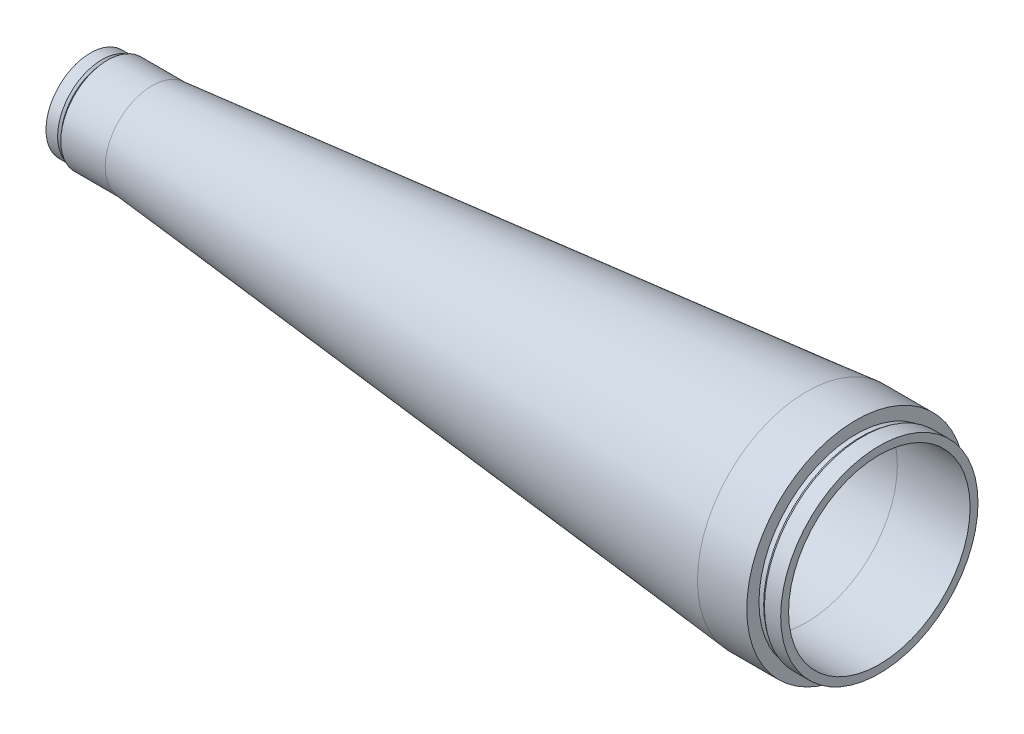
SolidWorks part; units mm, degrees
material "3.1645 (EN-AW 2030)"
ref_plane "Přední rovina" through (0, 0, 0) normal (0, 0, 1) x (1, 0, 0)
ref_plane "Horní rovina" through (0, 0, 0) normal (0, 1, 0) x (1, 0, 0)
ref_plane "Pravá rovina" through (0, 0, 0) normal (1, 0, 0) x (0, 0, -1)
sketch "Skica1" plane through (0, 0, 0) normal (0, 0, 1) x (1, 0, 0)
  line L0 (-36.7133, 44.25) -> (-36.7133, -44.25) construction
  line L1 (-36.7133, 44.25) -> (-36.7133, -38.9168) construction
  line L2 (-172.4424, 0) -> (-98.619, 0) construction
  line L3 (-36.7133, -44.25) -> (-56.7133, -44.25)
  line L7 (-322.05, -12.9) -> (-217.05, -23.4)
  line L9 (-212.6322, -25.6) -> (-117.05, -29.4)
  line L10 (-117.05, -29.4) -> (-117.05, -33.4)
  line L12 (-56.7133, -36.8) -> (-27.2133, -36.8)
  line L13 (-27.2133, -36.8) -> (-27.2133, -40)
  line L14 (-27.2133, -40) -> (-33.8133, -40)
  line L15 (-36.7133, -39.3) -> (-36.7133, -44.25)
  line L16 (-26.7133, 38.094) -> (-26.7133, -38.094) construction
  line L17 (-56.7133, -44.25) -> (-56.7133, -36.8) construction
  line L19 (-34.8133, -39.3) -> (-36.7133, -39.3)
  line L21 (-34.8133, -39.3) -> (-33.8133, -40)
  line L22 (-506.9511, 0) -> (94.0461, 0) construction
  line L23 (-115.55, -33.4) -> (-117.05, -33.4)
  line L24 (-117.05, 27.4) -> (-117.05, -27.4) construction
  line L27 (-112.0997, -33.4124) -> (-56.7133, -36.8)
  line L28 (-217.05, -19.7) -> (-217.05, 19.7) construction
  line L29 (-117.05, -27.4) -> (-115.05, -29.4) construction
  line L34 (-115.05, -33.4) -> (-117.05, -33.4) construction
  line L35 (-115.05, -33.4) -> (-115.05, -29.4) construction
  line L37 (-117.05, -33.4) -> (-117.05, -27.4) construction
  line L40 (-115.55, -33.4) -> (-115.55, -34.5)
  line L41 (-115.55, -34.5) -> (-113.1873, -34.5)
  line L42 (-113.1873, -34.5) -> (-112.0997, -33.4124)
  line L43 (-113.45, -34.1) -> (-113.45, -30.9) construction
  line L44 (-36.7133, -39.3) -> (-36.7133, -44.25) construction
  line L45 (-217.05, -23.4) -> (-217.05, -25.4)
  line L46 (-217.05, -25.4) -> (-215.55, -25.4)
  line L47 (-215.55, -25.4) -> (-215.55, -26.9)
  line L48 (-215.55, -26.9) -> (-213.9322, -26.9)
  line L49 (-213.9322, -26.9) -> (-212.6322, -25.6)
  line L50 (-217.05, -25.4) -> (-215.05, -25.4) construction
  line L51 (-215.05, -25.4) -> (-215.05, -21.7) construction
  line L52 (-215.05, -21.7) -> (-217.05, -19.7) construction
  line L53 (-217.05, -19.7) -> (-217.05, -25.4) construction
  line L54 (-213.8, -26.25) -> (-213.8, -23.75) construction
  line L55 (-347.05, -18) -> (-342.35, -18)
  line L56 (-322.05, -19) -> (-56.7133, -44.25)
  line L57 (-322.05, -9.65) -> (-322.05, 9.65) construction
  line L59 (-322.05, -12.9) -> (-322.05, -15.4)
  line L60 (-322.05, -15.4) -> (-323.75, -15.4)
  line L61 (-323.75, -15.4) -> (-323.75, -16.5)
  line L62 (-323.75, -16.5) -> (-324.9642, -16.5)
  line L63 (-324.9642, -16.5) -> (-325.9642, -15.5)
  line L64 (-325.9642, -15.5) -> (-345.05, -15.5)
  line L65 (-322.05, -15.4) -> (-322.05, -9.65) construction
  line L66 (-322.05, -9.65) -> (-324.05, -11.65) construction
  line L67 (-324.05, -11.65) -> (-324.05, -15.4) construction
  line L68 (-324.05, -15.4) -> (-322.05, -15.4) construction
  line L69 (-325.05, -16) -> (-325.05, -14) construction
  line L70 (-325.05, -15) -> (-325.9642, -15.5) construction
  line L71 (-347.05, 6) -> (-347.05, -6) construction
  line L72 (-347.05, -15.5) -> (-347.05, -18)
  line L75 (-345.05, -15.5) -> (-347.05, -15.5)
  line L76 (-340.05, -19) -> (-340.05, -17.3)
  line L77 (-340.05, -17.3) -> (-341.55, -17.3)
  line L78 (-341.55, -17.3) -> (-342.35, -18)
  line L79 (-340.05, -19) -> (-322.05, -19)
  arc A0 (-15.7133, 37.5) -> (-15.7133, -37.5) centre (509.65, 0) ccw construction
  arc A1 (-15.7133, 37.5) -> (-15.7133, -37.5) centre (509.65, 0) ccw construction
  circle A3 centre (-213.8, -25) radius 1.25 construction
  circle A4 centre (-113.45, -32.5) radius 1.6 construction
  circle A5 centre (-325.05, -15) radius 1 construction
  point P28 (-17.05, 0)
  point P31 (-217.05, 0)
  point P32 (-117.05, 0)
  point P55 (-322.05, 0)
  point P69 (-347.05, 0)
  dimension "D7" = 100
  dimension "D17" = 3.5
  dimension "D9" = 68.2
  dimension "D12" = 3.2
  dimension "D18" = 69
  dimension "D24" = 2.5
  dimension "D37" = 2
  dimension "D1" = 0.5
  dimension "D2" = 80
  dimension "D3" = 0.7
  dimension "D4" = 1.9
  dimension "D5" = 2.9
  dimension "D6" = 2.5
  dimension "D8" = 2
  dimension "D10" = 4
  dimension "D11" = 54.8
  dimension "D13" = 39.4
  dimension "D14" = 45
  dimension "D15" = 20
  dimension "D16" = 100
  dimension "D19" = 2
  dimension "D20" = 45
  dimension "D21" = 0.5
  dimension "D22" = 0.0124
  dimension "D23" = 52.5
  dimension "D25" = 45
  dimension "D26" = 45
  dimension "D27" = 2
  dimension "D28" = 0.2
  dimension "D29" = 1.5
  dimension "D30" = 2
  dimension "D31" = 53.8
  dimension "D32" = 0.5
  dimension "D33" = 36
  dimension "D34" = 105
  dimension "D35" = 19.3
  dimension "D36" = 31
  dimension "D38" = 45
  dimension "D39" = 2
  dimension "D40" = 32
  dimension "D41" = 0.3
  dimension "D42" = 0.1
  dimension "D43" = 38
  dimension "D44" = 2.5
  dimension "D45" = 33
  dimension "D46" = 45
  dimension "D47" = 330
  dimension "D48" = 12
  dimension "D49" = 1.5
  dimension "D50" = 2.3
  dimension "D51" = 0.7
  dimension "D52" = 7
revolve "Rotovat1" add sketch "Skica1" angle 360 about L2
cosmetic thread "Kosmetický závit2" parameters "D2"=34.92
